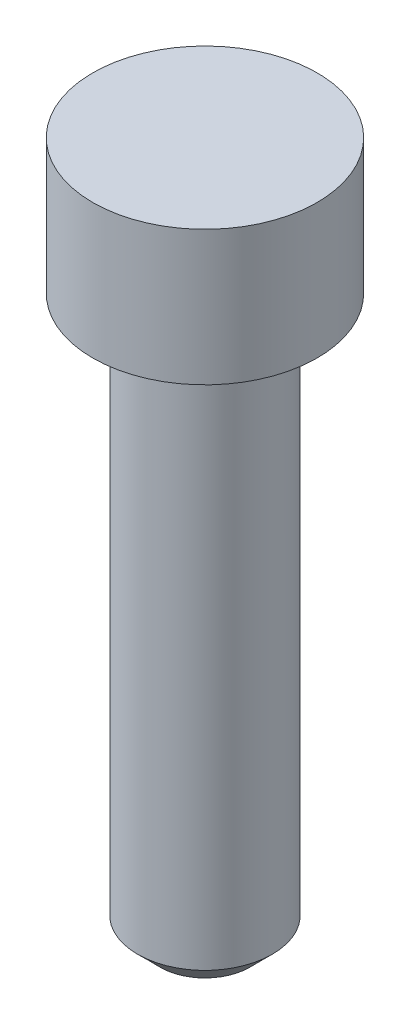
SolidWorks part; units mm, degrees
ref_plane "Front Plane" through (0, 0, 0) normal (0, 0, 1) x (1, 0, 0)
ref_plane "Top Plane" through (0, 0, 0) normal (0, 1, 0) x (1, 0, 0)
ref_plane "Right Plane" through (0, 0, 0) normal (1, 0, 0) x (0, 0, -1)
sketch "Sketch1" plane through (0, 0, 0) normal (0, 1, 0) x (1, 0, 0)
  circle A0 centre (0, 0) radius 5
  dimension "D1" = 10
extrude "Boss-Extrude1" add sketch "Sketch1" along normal blind 6
sketch "Sketch2" plane through (0, 0, 0) normal (0, -1, 0) x (1, 0, 0)
  circle A0 centre (0, 0) radius 3
extrude "Boss-Extrude2" add sketch "Sketch2" along normal blind 25
chamfer "Chamfer1" distance 1 angle 45 1 edges at (0, -25, -3)
